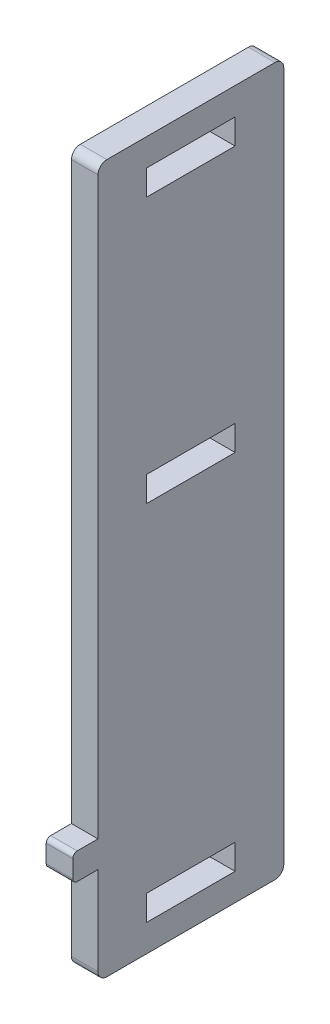
SolidWorks part; units mm, degrees
ref_plane "Спереди" through (0, 0, 0) normal (0, 0, 1) x (1, 0, 0)
ref_plane "Сверху" through (0, 0, 0) normal (0, 1, 0) x (1, 0, 0)
ref_plane "Справа" through (0, 0, 0) normal (1, 0, 0) x (0, 0, -1)
sketch "Эскиз1" plane through (0, 0, 0) normal (1, 0, 0) x (0, 0, -1)
  line L0 (-5, 6.925) -> (5, 6.925)
  line L1 (-10.5, -40) -> (10.5, -40)
  line L2 (-10.5, -40) -> (-10.5, -29)
  line L3 (-10.5, 40) -> (10.5, 40)
  line L4 (10.5, -40) -> (10.5, 40)
  line L5 (-10.5, -40) -> (10.5, 40) construction
  line L6 (-10.5, 40) -> (10.5, -40) construction
  line L7 (-5, -34.075) -> (5, -34.075)
  line L8 (-5, -34.075) -> (-5, -36.925)
  line L9 (-5, -36.925) -> (5, -36.925)
  line L10 (5, -34.075) -> (5, -36.925)
  line L11 (-5, -34.075) -> (5, -36.925) construction
  line L12 (-5, -36.925) -> (5, -34.075) construction
  line L13 (-5, 6.925) -> (-5, 4.075)
  line L14 (-5, 4.075) -> (5, 4.075)
  line L15 (5, 6.925) -> (5, 4.075)
  line L16 (-5, 6.925) -> (5, 4.075) construction
  line L17 (-5, 4.075) -> (5, 6.925) construction
  line L18 (-5, 36.925) -> (5, 36.925)
  line L19 (-5, 36.925) -> (-5, 34.075)
  line L20 (-5, 34.075) -> (5, 34.075)
  line L21 (5, 36.925) -> (5, 34.075)
  line L22 (-5, 36.925) -> (5, 34.075) construction
  line L23 (-5, 34.075) -> (5, 36.925) construction
  line L24 (-10.5, -26) -> (-10.5, 40)
  line L25 (-13.35, -26) -> (-10.5, -26)
  line L26 (-13.35, -26) -> (-13.35, -29)
  line L27 (-13.35, -29) -> (-10.5, -29)
  line L29 (-13.35, -26) -> (-10.5, -29) construction
  line L30 (-13.35, -29) -> (-10.5, -26) construction
  point P0 (0, 0)
  point P5 (0, 5.5)
  point P7 (0, -35.5)
  point P16 (0, 35.5)
  point P22 (-11.925, -27.5)
  dimension "D1" = 80
  dimension "D2" = 21
  dimension "D3" = 4.5
  dimension "D4" = 4.5
  dimension "D5" = 10
  dimension "D6" = 2.85
  dimension "D7" = 12.5
  dimension "D8" = 3
  dimension "D9" = 30
extrude "Бобышка-Вытянуть1" add sketch "Эскиз1" along normal blind 3 contours L3 L4 L1 L2 L27 L26 L25 L24
fillet "Скругление1" radius 1 4 edges at (1.5, 40, 10.5) (1.5, -40, 10.5) (1.5, 40, -10.5) (1.5, -40, -10.5)
fillet "Скругление2" radius 0.5 2 edges at (1.5, -29, 13.35) (1.5, -26, 13.35)
